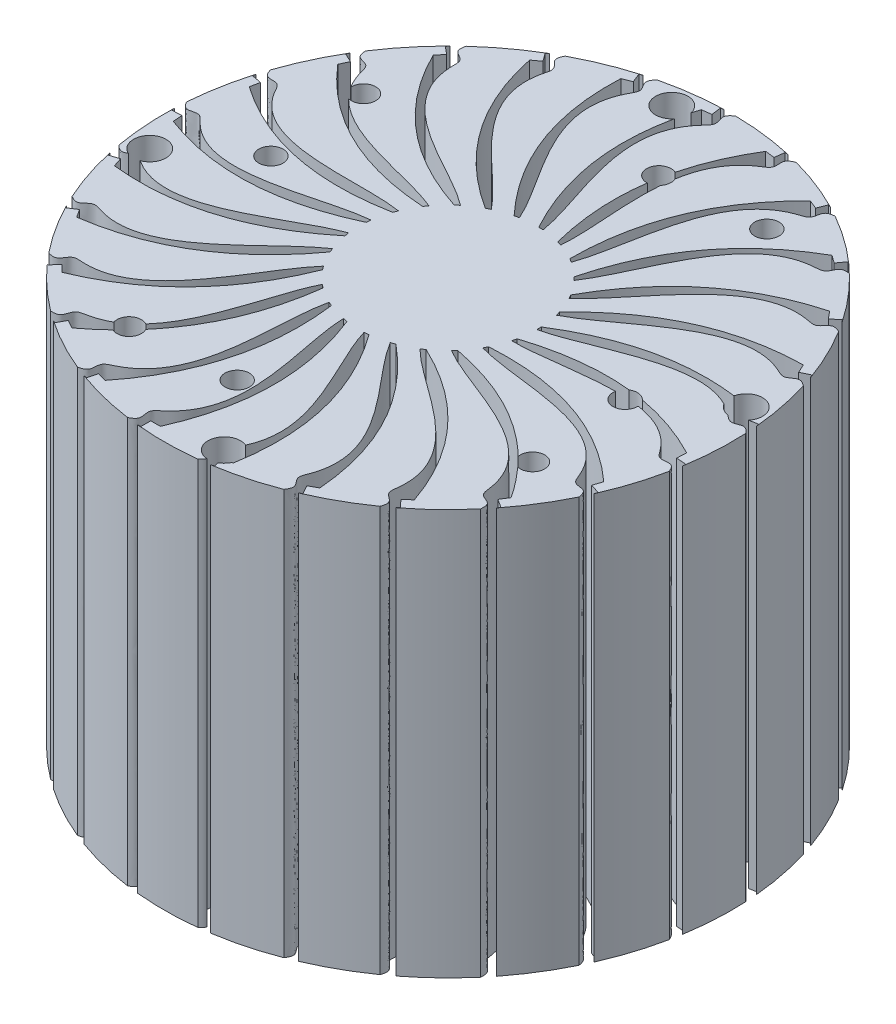
SolidWorks part; units mm, degrees
ref_plane "Front Plane" through (0, 0, 0) normal (0, 0, 1) x (1, 0, 0)
ref_plane "Top Plane" through (0, 0, 0) normal (0, 1, 0) x (1, 0, 0)
ref_plane "Right Plane" through (0, 0, 0) normal (1, 0, 0) x (0, 0, -1)
sketch "Sketch1" plane through (0, 0, 0) normal (0, 1, 0) x (1, 0, 0)
  line L0 (0, -35) -> (0, 35) construction
  line L1 (0, 35) -> (0, 0) construction
  line L2 (0, 0) -> (35, 0) construction
  line L3 (0, 0) -> (-35, 0) construction
  circle A0 centre (0, 0) radius 35
  circle A1 centre (0, 0) radius 24 construction
  point P6 (0, 0)
  dimension "D1" = 70
  dimension "D2" = 48
extrude "Boss-Extrude1" add sketch "Sketch1" along normal blind 50
hole_wizard "Ø3.0mm Dowel Hole1" positions "Sketch2" profile "Sketch3" hole size "Ø3.0" standard "ANSI Metric" end condition through all
sketch "Sketch2" plane through (0, 0, 0) normal (0, -1, 0) x (-1, 0, 0)
  circle A0 centre (0, 0) radius 24 construction
  point P5 (-2.0777, 23.9099)
  point P11 (23.9099, 2.0777)
  point P12 (2.0777, -23.9099)
  point P13 (-23.9099, -2.0777)
  dimension "D1" = 48
  dimension "D2" = 4
sketch "Sketch3" plane through (23.9099, 0, 2.0777) normal (1, 0, 0) x (0, 0, -1)
  line L0 (0, 0) -> (0, 50)
  line L1 (0, 50) -> (1.5, 50)
  line L2 (1.5, 50) -> (1.5, 0)
  line L5 (1.5, 0) -> (0, 0)
  line L11 (0, -6.35) -> (0, 107.95) construction
  dimension "Thru Hole Dia." = 3
  dimension "Thru Hole Depth" = 50
hole_wizard "Ø4.0mm Dowel Hole1" positions "Sketch4" profile "Sketch5" hole size "Ø4.0" standard "ANSI Metric" end condition through all
sketch "Sketch4" plane through (0, 50, 0) normal (0, 1, 0) x (1, 0, 0)
  circle A0 centre (0, 0) radius 32.5 construction
  point P6 (4.5927, -32.1739)
  point P12 (-32.1739, -4.5927)
  point P13 (-4.5927, 32.1739)
  point P14 (32.1739, 4.5927)
  dimension "D1" = 65
  dimension "D2" = 4
sketch "Sketch5" plane through (32.1739, 50, -4.5927) normal (1, 0, 0) x (0, 0, 1)
  line L0 (0, 0) -> (0, 50)
  line L1 (0, 50) -> (2, 50)
  line L2 (2, 50) -> (2, 0)
  line L5 (2, 0) -> (0, 0)
  line L11 (0, -6.35) -> (0, 107.95) construction
  dimension "Thru Hole Dia." = 4
  dimension "Thru Hole Depth" = 50
sketch "Sketch8" plane through (0, 0, 0) normal (0, -1, 0) x (1, 0, 0)
  line L0 (-24.6838, -22.8593) -> (-23.9344, -23.7668)
  line L1 (-23.9344, -23.7668) -> (-24.8725, -24.5415)
  line L2 (-29.5932, -16.0025) -> (-29.093, -17.0679)
  line L3 (-29.093, -17.0679) -> (-30.1943, -17.5849)
  line L4 (-32.6431, -8.1402) -> (-32.4236, -9.2965)
  line L5 (-32.4236, -9.2965) -> (-33.6188, -9.5235)
  line L6 (-33.642, 0.2336) -> (-33.7169, -0.9411)
  line L7 (-33.7169, -0.9411) -> (-34.931, -0.8636)
  line L8 (-32.527, 8.5927) -> (-32.8917, 7.4736)
  line L9 (-32.8917, 7.4736) -> (-34.0484, 7.8505)
  line L10 (-29.3682, 16.4118) -> (-29.9997, 15.4186)
  line L11 (-29.9997, 15.4186) -> (-31.0263, 16.0714)
  line L12 (-24.3641, 23.1998) -> (-25.2228, 22.3948)
  line L13 (-25.2228, 22.3948) -> (-26.0548, 23.2824)
  line L14 (-17.8291, 28.53) -> (-18.861, 27.9639)
  line L15 (-18.861, 27.9639) -> (-19.4462, 29.0305)
  line L16 (-10.1738, 32.0676) -> (-11.3141, 31.7759)
  line L17 (-11.3141, 31.7759) -> (-11.6156, 32.9545)
  line L18 (-1.8793, 33.5903) -> (-3.0563, 33.5913)
  line L19 (-3.0563, 33.5913) -> (-3.0552, 34.8079)
  line L20 (6.5333, 33.0023) -> (5.3935, 33.296)
  line L21 (5.3935, 33.296) -> (5.6971, 34.4741)
  line L22 (14.5354, 30.3407) -> (13.5045, 30.9086)
  line L23 (13.5045, 30.9086) -> (14.0915, 31.9743)
  line L24 (21.6242, 25.7727) -> (20.7669, 26.5792)
  line L25 (20.7669, 26.5792) -> (21.6005, 27.4653)
  line L26 (27.3542, 19.5853) -> (26.7244, 20.5796)
  line L27 (26.7244, 20.5796) -> (27.7522, 21.2306)
  line L28 (31.3655, 12.1673) -> (31.0028, 13.287)
  line L29 (31.0028, 13.287) -> (32.1601, 13.6619)
  line L30 (33.406, 3.9847) -> (33.3331, 5.1595)
  line L31 (33.3331, 5.1595) -> (34.5474, 5.2348)
  line L32 (33.3474, -4.4482) -> (33.569, -3.2922)
  line L33 (33.569, -3.2922) -> (34.7638, -3.5212)
  line L34 (31.1935, -12.6016) -> (31.6956, -11.5371)
  line L35 (31.6956, -11.5371) -> (32.796, -12.056)
  line L36 (27.0796, -19.9632) -> (27.8307, -19.057)
  line L37 (27.8307, -19.057) -> (28.7674, -19.8333)
  line L38 (21.2642, -26.0705) -> (22.2171, -25.3795)
  line L39 (22.2171, -25.3795) -> (22.9313, -26.3643)
  line L40 (14.1127, -30.5396) -> (15.2074, -30.1073)
  line L41 (15.2074, -30.1073) -> (15.6543, -31.2388)
  line L42 (6.0744, -33.0899) -> (7.2423, -32.9433)
  line L43 (7.2423, -32.9433) -> (7.3937, -34.1505)
  line L44 (-2.3455, -33.5609) -> (-1.1779, -33.7095)
  line L45 (-1.1779, -33.7095) -> (-1.3314, -34.9163)
  line L46 (-10.6181, -31.9232) -> (-9.5241, -32.3575)
  line L47 (-9.5241, -32.3575) -> (-9.9729, -33.4883)
  line L48 (-18.2235, -28.2797) -> (-17.2719, -28.9724)
  line L49 (-17.2719, -28.9724) -> (-17.9878, -29.956)
  circle A0 centre (0, 0) radius 11 construction
  circle A1 centre (0, 0) radius 35 construction
  spline S0 degree 2 poles (-7.3916, -8.1464) (-19.3939, -12.0677) (-24.6838, -22.8593) knots 0 0 0 1 1 1
  spline S1 degree 3 poles (-6.9739, -8.5068) (-11.6031, -12.1003) (-22.8368, -15.2745) (-22.2784, -24.2479) (-24.6573, -24.7361) (-22.6961, -27.4924) (-24.8725, -24.5415) knots 0 0 0 0 0.801044 0.845231 0.897133 1 1 1 1
  spline S2 degree 1 poles (-6.9739, -8.5068) (-7.3916, -8.1464) knots 0 0 1 1
  spline S3 degree 1 poles (-8.8703, -6.5052) (-9.1853, -6.0522) knots 0 0 1 1
  spline S4 degree 2 poles (-9.1853, -6.0522) (-21.7857, -6.8655) (-29.5932, -16.0025) knots 0 0 0 1 1 1
  spline S5 degree 3 poles (-8.8703, -6.5052) (-14.2478, -8.8346) (-25.918, -9.1153) (-27.6087, -17.9457) (-30.0342, -17.8269) (-28.8202, -20.9844) (-30.1943, -17.5849) knots 0 0 0 0 0.801044 0.845231 0.897133 1 1 1 1
  spline S6 degree 1 poles (-10.2094, -4.0948) (-10.4019, -3.5778) knots 0 0 1 1
  spline S7 degree 2 poles (-10.4019, -3.5778) (-22.8086, -1.2319) (-32.6431, -8.1402) knots 0 0 0 1 1 1
  spline S8 degree 3 poles (-10.2094, -4.0948) (-15.9973, -5.0137) (-27.3706, -2.3834) (-31.2042, -10.5159) (-33.524, -9.7976) (-33.1334, -13.1579) (-33.6188, -9.5235) knots 0 0 0 0 0.801044 0.845231 0.897133 1 1 1 1
  spline S9 degree 1 poles (-10.907, -1.4272) (-10.9649, -0.8785) knots 0 0 1 1
  spline S10 degree 2 poles (-10.9649, -0.8785) (-22.3984, 4.4791) (-33.642, 0.2336) knots 0 0 0 1 1 1
  spline S11 degree 3 poles (-10.907, -1.4272) (-16.7416, -0.8779) (-27.1035, 4.4983) (-32.8391, -2.4253) (-34.9074, -1.1527) (-35.3647, -4.5045) (-34.931, -0.8636) knots 0 0 0 0 0.801044 0.845231 0.897133 1 1 1 1
  spline S12 degree 1 poles (-10.9193, 1.3301) (-10.8389, 1.8759) knots 0 0 1 1
  spline S13 degree 2 poles (-10.8389, 1.8759) (-20.5808, 9.9086) (-32.527, 8.5927) knots 0 0 0 1 1 1
  spline S14 degree 3 poles (-10.9193, 1.3301) (-16.4339, 3.3132) (-25.1333, 11.0973) (-32.4106, 5.8176) (-34.0974, 7.5646) (-35.3738, 4.4318) (-34.0484, 7.8505) knots 0 0 0 0 0.801044 0.845231 0.897133 1 1 1 1
  spline S15 degree 1 poles (-10.2455, 4.0038) (-10.0318, 4.5125) knots 0 0 1 1
  spline S16 degree 2 poles (-10.0318, 4.5125) (-17.4701, 14.7156) (-29.3682, 16.4118) knots 0 0 0 1 1 1
  spline S17 degree 3 poles (-10.2455, 4.0038) (-15.0937, 7.296) (-21.5839, 16.9991) (-29.9455, 13.695) (-31.1449, 15.8066) (-33.1604, 13.0897) (-31.0263, 16.0714) knots 0 0 0 0 0.801044 0.845231 0.897133 1 1 1 1
  spline S18 degree 1 poles (-8.9279, 6.426) (-8.5944, 6.8655) knots 0 0 1 1
  spline S19 degree 2 poles (-8.5944, 6.8655) (-13.2616, 18.5979) (-24.3641, 23.1998) knots 0 0 0 1 1 1
  spline S20 degree 3 poles (-8.9279, 6.426) (-12.805, 10.8205) (-16.6783, 21.8327) (-25.5989, 20.7119) (-26.2355, 23.0554) (-28.8633, 20.9251) (-26.0548, 23.2824) knots 0 0 0 0 0.801044 0.845231 0.897133 1 1 1 1
  spline S21 degree 1 poles (-7.0493, 8.4444) (-6.617, 8.7872) knots 0 0 1 1
  spline S22 degree 2 poles (-6.617, 8.7872) (-8.2199, 21.3116) (-17.8291, 28.53) knots 0 0 0 1 1 1
  spline S23 degree 3 poles (-7.0493, 8.4444) (-9.7118, 13.665) (-10.7247, 25.2945) (-19.6439, 26.4274) (-19.6776, 28.8556) (-22.7526, 27.4457) (-19.4462, 29.0305) knots 0 0 0 0 0.801044 0.845231 0.897133 1 1 1 1
  spline S24 degree 1 poles (-4.7278, 9.9322) (-4.2239, 10.1567) knots 0 0 1 1
  spline S25 degree 2 poles (-4.2239, 10.1567) (-2.6616, 22.6863) (-10.1738, 32.0676) knots 0 0 0 1 1 1
  spline S26 degree 3 poles (-4.7278, 9.9322) (-6.0083, 15.6509) (-4.0973, 27.167) (-12.4545, 30.4824) (-11.8833, 32.8427) (-15.2124, 32.2418) (-11.6156, 32.9545) knots 0 0 0 0 0.801044 0.845231 0.897133 1 1 1 1
  spline S27 degree 1 poles (-2.1093, 10.7959) (-1.5653, 10.8881) knots 0 0 1 1
  spline S28 degree 2 poles (-1.5653, 10.8881) (3.0638, 22.6354) (-1.8793, 33.5903) knots 0 0 0 1 1 1
  spline S29 degree 3 poles (-2.1093, 10.7959) (-1.9273, 16.6534) (2.7876, 27.3324) (-4.4825, 32.622) (-3.3423, 34.7661) (-6.7162, 35.012) (-3.0552, 34.8079) knots 0 0 0 0 0.801044 0.845231 0.897133 1 1 1 1
  spline S30 degree 1 poles (0.6418, 10.9813) (1.1916, 10.9353) knots 0 0 1 1
  spline S31 degree 2 poles (1.1916, 10.9353) (8.5968, 21.1624) (6.5333, 33.0023) knots 0 0 0 1 1 1
  spline S32 degree 3 poles (0.6418, 10.9813) (2.2747, 16.6095) (9.4973, 25.7805) (3.771, 32.7119) (5.4087, 34.5051) (2.2019, 35.5823) (5.6971, 34.4741) knots 0 0 0 0 0.801044 0.845231 0.897133 1 1 1 1
  spline S33 degree 1 poles (3.3526, 10.4766) (3.8737, 10.2954) knots 0 0 1 1
  spline S34 degree 2 poles (3.8737, 10.2954) (13.5896, 18.3596) (14.5354, 30.3407) knots 0 0 0 1 1 1
  spline S35 degree 3 poles (3.3526, 10.4766) (6.3339, 15.522) (15.6102, 22.6087) (11.7877, 30.7464) (13.8198, 32.076) (10.9817, 33.9168) (14.0915, 31.9743) knots 0 0 0 0 0.801044 0.845231 0.897133 1 1 1 1
  spline S36 degree 1 poles (5.8527, 9.3137) (6.3123, 9.0086) knots 0 0 1 1
  spline S37 degree 2 poles (6.3123, 9.0086) (17.7285, 14.4032) (21.6242, 25.7727) knots 0 0 0 1 1 1
  spline S38 degree 3 poles (5.8527, 9.3137) (9.9951, 13.4592) (20.7424, 18.0163) (19.0637, 26.8489) (21.3626, 27.6314) (19.0715, 30.1202) (21.6005, 27.4653) knots 0 0 0 0 0.801044 0.845231 0.897133 1 1 1 1
  spline S39 degree 1 poles (7.9851, 7.5656) (8.3544, 7.1557) knots 0 0 1 1
  spline S40 degree 2 poles (8.3544, 7.1557) (20.7534, 9.5418) (27.3542, 19.5853) knots 0 0 0 1 1 1
  spline S41 degree 3 poles (7.9851, 7.5656) (13.0282, 10.5506) (24.5712, 12.2918) (25.1418, 21.2645) (27.5631, 21.4506) (25.9629, 24.4311) (27.7522, 21.2306) knots 0 0 0 0 0.801044 0.845231 0.897133 1 1 1 1
  spline S42 degree 1 poles (9.6157, 5.3421) (9.8715, 4.8533) knots 0 0 1 1
  spline S43 degree 2 poles (9.8715, 4.8533) (22.4744, 4.0809) (31.3655, 12.1673) knots 0 0 0 1 1 1
  spline S44 degree 3 poles (9.6157, 5.3421) (15.2427, 6.9792) (26.8561, 5.7951) (29.6402, 14.3439) (32.0317, 13.9221) (31.223, 17.2068) (32.1601, 13.6619) knots 0 0 0 0 0.801044 0.845231 0.897133 1 1 1 1
  spline S45 degree 1 poles (10.6421, 2.783) (10.7683, 2.2459) knots 0 0 1 1
  spline S46 degree 2 poles (10.7683, 2.2459) (22.7832, -1.6365) (33.406, 3.9847) knots 0 0 0 1 1 1
  spline S47 degree 3 poles (10.6421, 2.783) (16.4995, 2.9692) (27.4535, -1.0658) (32.2762, 6.522) (34.4877, 5.5187) (34.5212, 8.9014) (34.5474, 5.2348) knots 0 0 0 0 0.801044 0.845231 0.897133 1 1 1 1
  spline S48 degree 1 poles (10.9999, 0.0489) (10.9885, -0.5026) knots 0 0 1 1
  spline S49 degree 2 poles (10.9885, -0.5026) (21.6604, -7.251) (33.3474, -4.4482) knots 0 0 0 1 1 1
  spline S50 degree 3 poles (10.9999, 0.0489) (16.7196, -1.2273) (26.326, -7.8598) (32.8841, -1.7096) (34.7766, -3.2314) (35.6504, 0.0367) (34.7638, -3.5212) knots 0 0 0 0 0.801044 0.845231 0.897133 1 1 1 1
  spline S51 degree 1 poles (10.6665, -2.6882) (10.5183, -3.2196) knots 0 0 1 1
  spline S52 degree 2 poles (10.5183, -3.2196) (19.1766, -12.4099) (31.1935, -12.6016) knots 0 0 0 1 1 1
  spline S53 degree 3 poles (10.6665, -2.6882) (15.8891, -5.3468) (23.5442, -14.1598) (31.4258, -9.8339) (32.8804, -11.7785) (34.5395, -8.8304) (32.796, -12.056) knots 0 0 0 0 0.801044 0.845231 0.897133 1 1 1 1
  spline S54 degree 1 poles (9.6629, -5.2563) (9.3872, -5.7342) knots 0 0 1 1
  spline S55 degree 2 poles (9.3872, -5.7342) (15.488, -16.7891) (27.0796, -19.9632) knots 0 0 0 1 1 1
  spline S56 degree 3 poles (9.6629, -5.2563) (14.0602, -9.1302) (19.2831, -19.5702) (27.993, -17.3402) (28.9182, -19.5855) (31.2583, -17.1426) (28.7674, -19.8333) knots 0 0 0 0 0.801044 0.845231 0.897133 1 1 1 1
  spline S57 degree 1 poles (8.0521, -7.4943) (7.6662, -7.8886) knots 0 0 1 1
  spline S58 degree 2 poles (7.6662, -7.8886) (10.8261, -20.1133) (21.2642, -26.0705) knots 0 0 0 1 1 1
  spline S59 degree 3 poles (8.0521, -7.4943) (11.3479, -12.34) (13.8104, -23.7509) (22.8012, -23.757) (23.139, -26.1618) (26.0131, -24.3776) (22.9313, -26.3643) knots 0 0 0 0 0.801044 0.845231 0.897133 1 1 1 1
  spline S60 degree 1 poles (5.9354, -9.2613) (5.4635, -9.5472) knots 0 0 1 1
  spline S61 degree 2 poles (5.4635, -9.5472) (5.484, -22.1738) (14.1127, -30.5396) knots 0 0 0 1 1 1
  spline S62 degree 3 poles (5.9354, -9.2613) (7.9225, -14.7744) (7.4699, -26.4392) (16.1767, -28.681) (15.9059, -31.0943) (19.1334, -30.081) (15.6543, -31.2388) knots 0 0 0 0 0.801044 0.845231 0.897133 1 1 1 1
  spline S63 degree 1 poles (3.4457, -10.4464) (2.9176, -10.606) knots 0 0 1 1
  spline S64 degree 2 poles (2.9176, -10.606) (-0.2027, -22.841) (6.0744, -33.0899) knots 0 0 0 1 1 1
  spline S65 degree 3 poles (3.4457, -10.4464) (3.9994, -16.2805) (0.6601, -27.4663) (8.5358, -31.803) (7.6733, -34.0731) (11.0514, -33.8942) (7.3937, -34.1505) knots 0 0 0 0 0.801044 0.845231 0.897133 1 1 1 1
  spline S66 degree 1 poles (0.7395, -10.9751) (0.1883, -10.9984) knots 0 0 1 1
  spline S67 degree 2 poles (0.1883, -10.9984) (-5.8767, -22.073) (-2.3455, -33.5609) knots 0 0 0 1 1 1
  spline S68 degree 3 poles (0.7395, -10.9751) (-0.1751, -16.7636) (-6.1912, -26.7675) (0.3586, -32.9266) (-1.0414, -34.9109) (2.2751, -35.5777) (-1.3314, -34.9163) knots 0 0 0 0 0.801044 0.845231 0.897133 1 1 1 1
  spline S69 degree 1 poles (-2.0131, -10.8142) (-2.5528, -10.6997) knots 0 0 1 1
  spline S70 degree 2 poles (-2.5528, -10.6997) (-11.1813, -19.918) (-10.6181, -31.9232) knots 0 0 0 1 1 1
  spline S71 degree 3 poles (-2.0131, -10.8142) (-4.3385, -16.1934) (-12.6535, -24.3869) (-7.8412, -31.9813) (-9.6907, -33.5551) (-6.6442, -35.0258) (-9.9729, -33.4883) knots 0 0 0 0 0.801044 0.845231 0.897133 1 1 1 1
  spline S72 degree 1 poles (-4.6392, -9.9738) (-5.1335, -9.7287) knots 0 0 1 1
  spline S73 degree 2 poles (-5.1335, -9.7287) (-15.7835, -16.5116) (-18.2235, -28.2797) knots 0 0 0 1 1 1
  spline S74 degree 3 poles (-4.6392, -9.9738) (-8.2294, -14.6057) (-18.3208, -20.4739) (-15.5483, -29.0265) (-17.731, -30.0909) (-15.146, -32.273) (-17.9878, -29.956) knots 0 0 0 0 0.801044 0.845231 0.897133 1 1 1 1
  point P283 (0, 0)
  dimension "D1" = 22
  dimension "D2" = 25
extrude "Cut-Extrude1" cut sketch "Sketch8" against normal blind 50
hole_wizard "Ø3.0mm Dowel Hole2" positions "Sketch9" profile "Sketch10" hole size "Ø3.0" standard "ANSI Metric" end condition through all
sketch "Sketch9" plane through (0, 50, 0) normal (0, 1, 0) x (1, 0, 0)
  circle A0 centre (0, 0) radius 28.75 construction
  point P5 (14.4434, 24.8586)
  point P11 (24.8586, -14.4434)
  point P12 (-14.4434, -24.8586)
  point P13 (-24.8586, 14.4434)
  dimension "D1" = 57.5
  dimension "D2" = 4
sketch "Sketch10" plane through (-24.8586, 50, -14.4434) normal (1, 0, 0) x (0, 0, 1)
  line L0 (0, 0) -> (0, 50)
  line L1 (0, 50) -> (1.5, 50)
  line L2 (1.5, 50) -> (1.5, 0)
  line L5 (1.5, 0) -> (0, 0)
  line L11 (0, -6.35) -> (0, 107.95) construction
  dimension "Thru Hole Dia." = 3
  dimension "Thru Hole Depth" = 50
